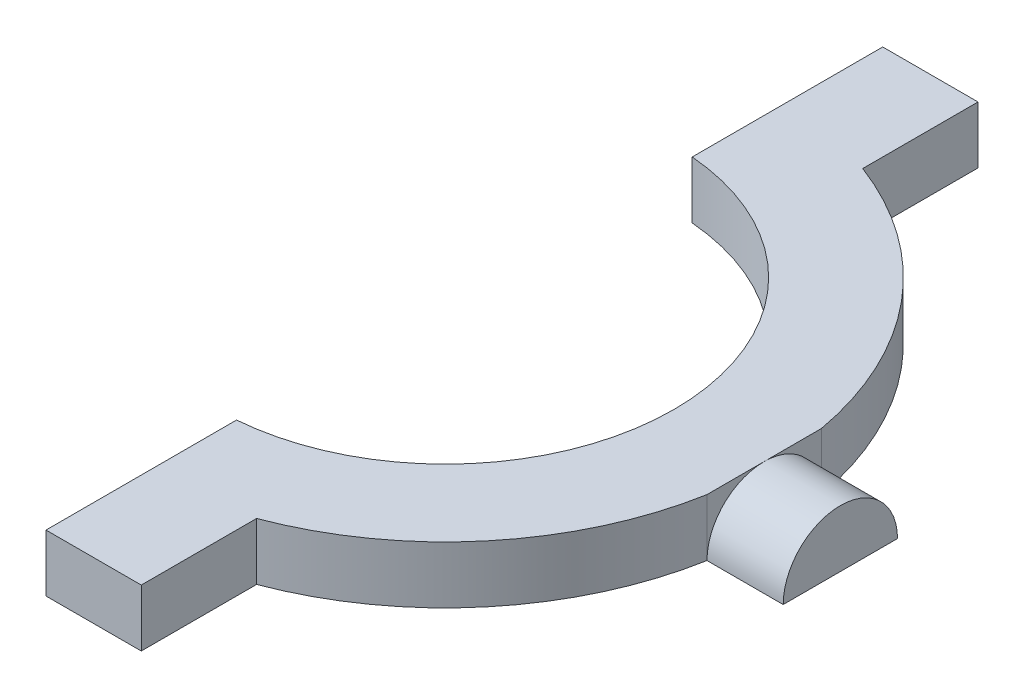
SolidWorks part; units mm, degrees
ref_plane "Front Plane" through (0, 0, 0) normal (0, 0, 1) x (1, 0, 0)
ref_plane "Top Plane" through (0, 0, 0) normal (0, 1, 0) x (1, 0, 0)
ref_plane "Right Plane" through (0, 0, 0) normal (1, 0, 0) x (0, 0, -1)
sketch "Sketch1" plane through (0, 0, 0) normal (0, 1, 0) x (1, 0, 0)
  line L0 (2, 43.9165) -> (2, 23.9165)
  line L1 (2, -23.9165) -> (2, -43.9165)
  line L2 (2, 43.9165) -> (12, 43.9165)
  line L3 (12, 43.9165) -> (12, 31.8119)
  line L4 (2, -43.9165) -> (12, -43.9165)
  line L5 (12, -43.9165) -> (12, -31.8119)
  line L7 (33.4664, -6) -> (41.4664, -6)
  line L9 (33.4664, 6) -> (41.4664, 6)
  line L10 (41.4664, -6) -> (41.4664, 6)
  arc A0 (2, -23.9165) -> (2, 23.9165) centre (0, 0) ccw
  arc A1 (12, -31.8119) -> (33.4664, -6) centre (0, 0) ccw
  arc A2 (33.4664, 6) -> (12, 31.8119) centre (0, 0) ccw
  point P13 (0, 0)
  dimension "D1" = 48
  dimension "D4" = 10
  dimension "D2" = 2
  dimension "D3" = 10
  dimension "D5" = 20
  dimension "D6" = 20
  dimension "D7" = 10
  dimension "D8" = 8
  dimension "D9" = 12
  dimension "D10" = 6
extrude "Boss-Extrude1" add sketch "Sketch1" along normal blind 6
sketch "Sketch2" plane through (41.4664, 0, 0) normal (1, 0, 0) x (0, 0, -1)
  line L0 (-6, 0) -> (6, 0)
  arc A0 (6, 0) -> (-6, 0) centre (0, 0) ccw
extrude "Cut-Extrude1" cut sketch "Sketch2" against normal blind 8 flip side to cut
